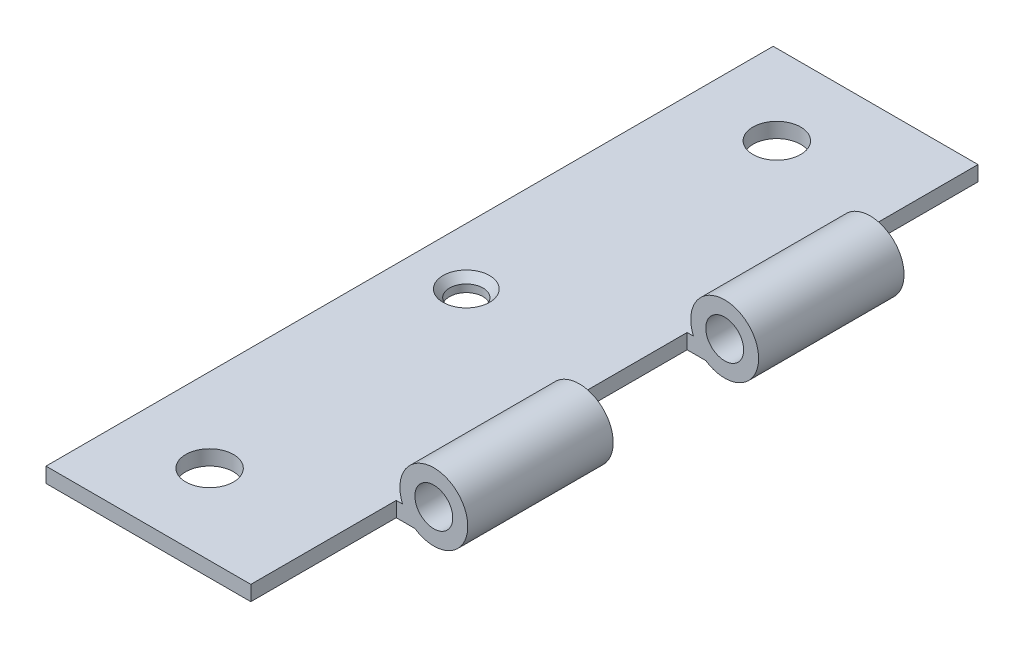
SolidWorks part; units mm, degrees
ref_plane "Front Plane" through (0, 0, 0) normal (0, 0, 1) x (1, 0, 0)
ref_plane "Top Plane" through (0, 0, 0) normal (0, 1, 0) x (1, 0, 0)
ref_plane "Right Plane" through (0, 0, 0) normal (1, 0, 0) x (0, 0, -1)
ref_plane "Plane1" through (0, 0, -7.62) normal (0, 0, 1) x (1, 0, 0)
sketch "Sketch1" plane through (0, 0, -7.62) normal (0, 0, 1) x (1, 0, 0)
  line L0 (-3.279, -1.376) -> (-3.279, -2.9508)
  line L1 (-3.279, -2.9508) -> (-1.9844, -2.9508)
  arc A0 (-1.9844, -2.9508) -> (-3.279, -1.376) centre (0, 0) ccw
extrude "Boss-Extrude1" add sketch "Sketch1" against normal blind 15.24
sketch "Sketch2" plane through (-3.279, 0, 0) normal (-1, 0, 0) x (0, 0, 1)
  line L0 (-7.62, -1.376) -> (-7.62, -2.9508)
  line L1 (-7.62, -2.9508) -> (-22.86, -2.9508)
  line L2 (-22.86, -2.9508) -> (-22.86, -1.376)
  line L3 (-22.86, -1.376) -> (-7.62, -1.376)
extrude "Boss-Extrude2" add sketch "Sketch2" along normal blind 0.2546
sketch "Sketch3" plane through (-3.5336, 0, 0) normal (-1, 0, 0) x (0, 0, 1)
  line L0 (7.62, -1.376) -> (7.62, -2.9508)
  line L1 (7.62, -2.9508) -> (-22.86, -2.9508)
  line L2 (-22.86, -2.9508) -> (-22.86, -1.376)
  line L3 (-22.86, -1.376) -> (7.62, -1.376)
extrude "Boss-Extrude3" add sketch "Sketch3" along normal blind 21.8664
sketch "Sketch4" plane through (-3.5336, 0, 0) normal (1, 0, 0) x (0, 0, -1)
  line L0 (-7.62, -1.376) -> (-7.62, -2.9508)
  line L1 (-7.62, -2.9508) -> (7.62, -2.9508)
  line L2 (7.62, -2.9508) -> (7.62, -1.376)
  line L3 (7.62, -1.376) -> (-7.62, -1.376)
extrude "Cut-Extrude1" cut sketch "Sketch4" against normal blind 0.4034
sketch "Sketch5" plane through (0, 0, 7.62) normal (0, 0, 1) x (1, 0, 0)
  line L0 (-25.4, -1.376) -> (-3.279, -1.376)
  line L1 (-1.9844, -2.9508) -> (-25.4, -2.9508)
  line L2 (-25.4, -2.9508) -> (-25.4, -1.376)
  arc A0 (-3.279, -1.376) -> (-1.9844, -2.9508) centre (0, 0) cw
extrude "Boss-Extrude4" add sketch "Sketch5" along normal blind 15.24
sketch "Sketch6" plane through (0, 0, 22.86) normal (0, 0, 1) x (1, 0, 0)
  line L0 (-25.4, -2.9508) -> (-25.4, -1.376)
  line L1 (-25.4, -1.376) -> (-3.937, -1.376)
  line L2 (-3.937, -1.376) -> (-3.937, -2.9508)
  line L3 (-3.937, -2.9508) -> (-25.4, -2.9508)
extrude "Boss-Extrude5" add sketch "Sketch6" along normal blind 15.24
sketch "Sketch7" plane through (0, 0, -22.86) normal (0, 0, -1) x (-1, 0, 0)
  line L0 (25.4, -1.376) -> (25.4, -2.9508)
  line L1 (25.4, -2.9508) -> (3.937, -2.9508)
  line L2 (3.937, -2.9508) -> (3.937, -1.376)
  line L3 (3.937, -1.376) -> (25.4, -1.376)
extrude "Boss-Extrude6" add sketch "Sketch7" along normal blind 15.24
hole_wizard "M3.5 Clearance Hole1" positions "Sketch9" profile "Sketch8" hole size "M3.5" standard "ANSI Metric"
sketch "Sketch9" plane through (0, 0, 7.62) normal (0, 0, -1) x (-1, 0, 0)
  point P0 (0, 0)
sketch "Sketch8" plane through (0, 0, 7.62) normal (1, 0, 0) x (0, 1, 0)
  line L0 (0, 0) -> (0, 30.48)
  line L1 (0, 30.48) -> (1.9844, 30.48)
  line L2 (1.9844, 30.48) -> (1.9844, 0)
  line L5 (1.9844, 0) -> (0, 0)
  line L11 (0, -6.35) -> (0, 107.95) construction
  dimension "Thru Hole Dia." = 3.9688
  dimension "Thru Hole Depth" = 30.48
hole_wizard "M3.5 Clearance Hole2" positions "Sketch11" profile "Sketch10" hole size "M3.5" standard "ANSI Metric"
sketch "Sketch11" plane through (0, 0, -22.86) normal (0, 0, -1) x (-1, 0, 0)
  point P0 (0, 0)
sketch "Sketch10" plane through (0, 0, -22.86) normal (1, 0, 0) x (0, 1, 0)
  line L0 (0, 0) -> (0, 60.96)
  line L1 (0, 60.96) -> (1.9844, 60.96)
  line L2 (1.9844, 60.96) -> (1.9844, 0)
  line L5 (1.9844, 0) -> (0, 0)
  line L11 (0, -6.35) -> (0, 107.95) construction
  dimension "Thru Hole Dia." = 3.9688
  dimension "Thru Hole Depth" = 60.96
hole_wizard "CSK for M3 Flat Head Machine Screw1" positions "Sketch13" profile "Sketch12" countersink size "M3" standard "ANSI Metric"
sketch "Sketch13" plane through (0, -1.376, 0) normal (0, 1, 0) x (1, 0, 0)
  point P0 (-16.637, 29.718)
  point P1 (-16.637, -29.718)
  point P2 (-19.4564, 0)
sketch "Sketch12" plane through (-16.637, -1.376, -29.718) normal (1, 0, 0) x (0, 0, 1)
  line L0 (0, 0) -> (0, 2.18)
  line L1 (0, 2.18) -> (1.7526, 2.18)
  line L2 (1.7526, 2.18) -> (1.7526, 0.7874)
  line L3 (1.7526, 0.7874) -> (2.4371, 0)
  line L5 (2.4371, 0) -> (0, 0)
  line L6 (-1.7526, 0.7874) -> (-2.4371, 0) construction
  line L11 (0, -6.35) -> (0, 107.95) construction
  dimension "Thru Hole Dia." = 3.5052
  dimension "Thru Hole Depth" = 2.18
  dimension "Near C'Sink Dia." = 4.8742
  dimension "Near C'Sink Angle" = 82
sketch "Sketch14" plane through (0, -1.376, 0) normal (0, 1, 0) x (1, 0, 0)
  circle A0 centre (-16.637, 29.718) radius 2.5
  circle A1 centre (-16.637, -29.718) radius 2.5
  dimension "D1" = 5
  dimension "D2" = 5
extrude "Cut-Extrude2" cut sketch "Sketch14" against normal up to surface (1.5748 mm away) up to face at (-14.8844, -2.9508, -29.718)
